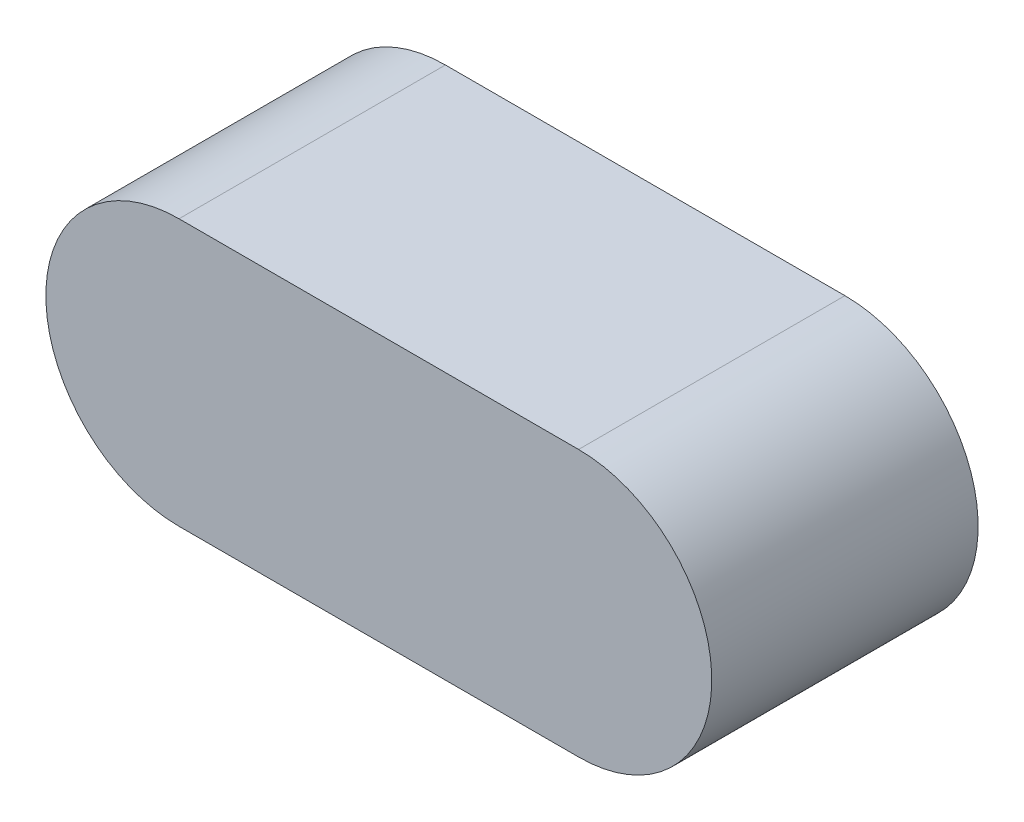
SolidWorks part; units mm, degrees
ref_plane "Front Plane" through (0, 0, 0) normal (0, 0, 1) x (1, 0, 0)
ref_plane "Top Plane" through (0, 0, 0) normal (0, 1, 0) x (1, 0, 0)
ref_plane "Right Plane" through (0, 0, 0) normal (1, 0, 0) x (0, 0, -1)
sketch "Sketch1" plane through (0, 0, 0) normal (0, 0, 1) x (1, 0, 0)
  line L0 (0, 0) -> (6, 0) construction
  line L1 (0, 2) -> (6, 2)
  line L2 (0, -2) -> (6, -2)
  arc A0 (0, 2) -> (0, -2) centre (0, 0) ccw
  arc A1 (6, -2) -> (6, 2) centre (6, 0) ccw
  point P3 (3, 0)
  dimension "D1" = 4
  dimension "D2" = 6
extrude "Boss-Extrude1" add sketch "Sketch1" along normal blind 4
